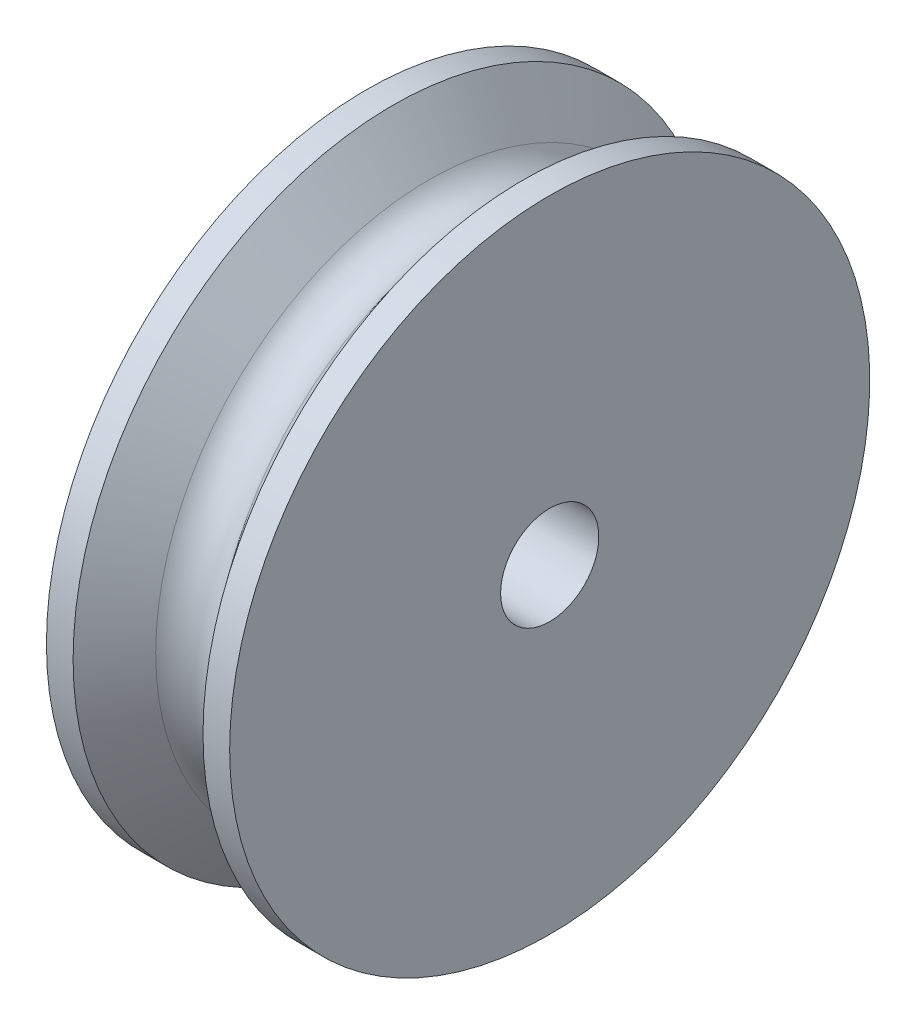
SolidWorks part; units mm, degrees
material "PET"
ref_plane "Front" through (0, 0, 0) normal (0, 0, 1) x (1, 0, 0)
ref_plane "Top" through (0, 0, 0) normal (0, 1, 0) x (1, 0, 0)
ref_plane "Right" through (0, 0, 0) normal (1, 0, 0) x (0, 0, -1)
sketch "Sketch1" plane through (0, 0, 0) normal (0, 0, 1) x (1, 0, 0)
  line L0 (0, 0) -> (5.8583, 0) construction
  line L1 (0, 2.5527) -> (9.525, 2.5527)
  line L2 (9.525, 2.5527) -> (9.525, 16.637)
  line L3 (9.525, 16.637) -> (8.1382, 16.637)
  line L4 (8.1382, 16.637) -> (6.2738, 14.2073)
  line L5 (3.2512, 14.2073) -> (1.3868, 16.637)
  line L6 (1.3868, 16.637) -> (0, 16.637)
  line L7 (0, 16.637) -> (0, 2.5527)
  arc A0 (6.2738, 14.2073) -> (3.2512, 14.2073) centre (4.7625, 15.367) cw
  dimension "D1" = 26.924
  dimension "D2" = 3.81
  dimension "D3" = 3.175
  dimension "D4" = 5.1054
  dimension "D5" = 75
  dimension "D6" = 9.525
revolve "Revolve1" add sketch "Sketch1" angle 360 about L0
